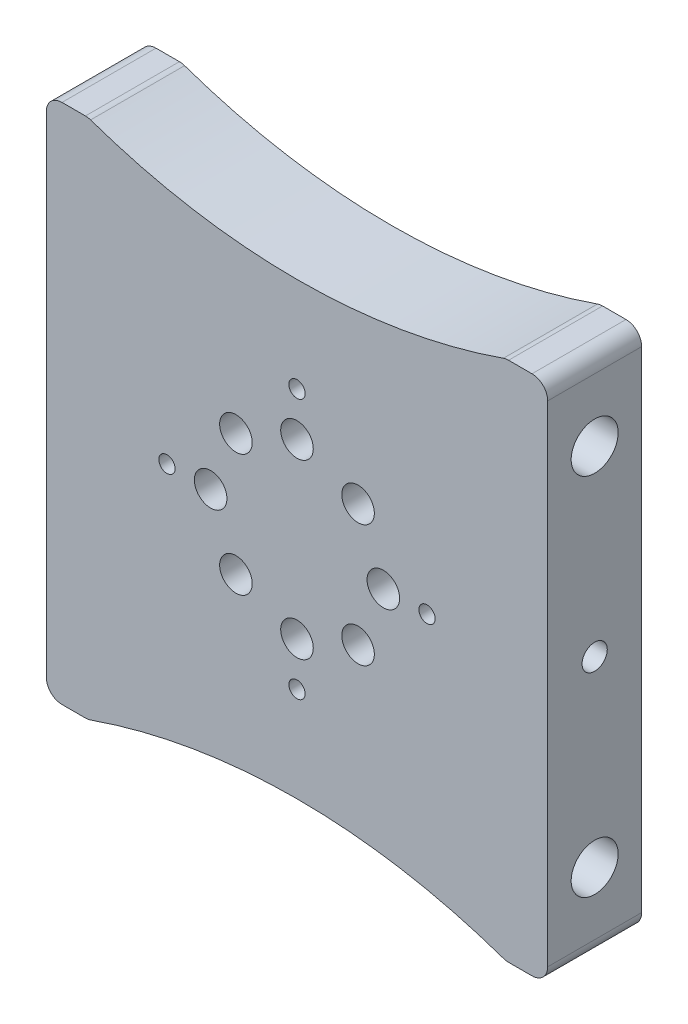
SolidWorks part; units mm, degrees
other "Markup2"
sketch "Sketch39"
material "Onyx"
ref_plane "Front Plane" through (0, 0, 0) normal (0, 0, 1) x (1, 0, 0)
ref_plane "Top Plane" through (0, 0, 0) normal (0, 1, 0) x (1, 0, 0)
ref_plane "Right Plane" through (0, 0, 0) normal (1, 0, 0) x (0, 0, -1)
ref_plane "Plane1" through (0, 0, 0) normal (0, 0, -1) x (-1, 0, 0)
sketch "Sketch1" plane through (0, 0, 0) normal (0, 0, -1) x (-1, 0, 0)
  line L0 (44.45, 0) -> (44.45, 60)
  line L1 (44.45, 60) -> (-44.45, 60)
  line L2 (-44.45, 60) -> (-44.45, 0)
  arc A0 (-44.45, 0) -> (44.45, 0) centre (0, 0) ccw
extrude "Boss-Extrude1" add sketch "Sketch1" against normal blind 19.05
hole_wizard "#4 Clearance Hole1" [suppressed] positions "Sketch3" profile "Sketch2" hole size "#4" standard "ANSI Inch"
sketch "Sketch3" plane through (0, 0, 19.05) normal (0, 0, 1) x (1, 0, 0)
  line L0 (6, 0) -> (6, 26.35) construction
  line L1 (6, 0) -> (32.35, 0) construction
  line L2 (6, 0) -> (6, -26.35) construction
  line L3 (6, 0) -> (-20.35, 0) construction
  circle A0 centre (6, 0) radius 26.35 construction
  point P0 (32.35, 0.009)
  point P1 (6, -26.35)
  point P2 (-20.35, -0.01)
  point P3 (6, 26.35)
  dimension "D1" = 52.7
  dimension "D2" = 6
sketch "Sketch2" plane through (32.35, 0.009, 19.05) normal (1, 0, 0) x (0, -1, 0)
  line L0 (0, 0) -> (0, 19.05)
  line L1 (0, 19.05) -> (1.65, 19.05)
  line L2 (1.65, 19.05) -> (1.65, 0)
  line L5 (1.65, 0) -> (0, 0)
  line L11 (0, -6.35) -> (0, 107.95) construction
  dimension "Thru Hole Dia." = 3.3
  dimension "Thru Hole Depth" = 19.05
hole_wizard "1/4 Clearance Hole1" [suppressed] positions "Sketch5" profile "Sketch4" hole size "1/4" standard "ANSI Inch"
sketch "Sketch5" plane through (0, 0, 0) normal (0, 0, -1) x (-1, 0, 0)
  point P0 (8.85, 30)
  point P1 (23.65, 38)
  point P2 (23.65, 22)
sketch "Sketch4" plane through (-8.85, 30, 0) normal (1, 0, 0) x (0, 1, 0)
  line L0 (0, 0) -> (0, 12.7)
  line L1 (0, 12.7) -> (3.3, 12.7)
  line L2 (3.3, 12.7) -> (3.3, 0)
  line L5 (3.3, 0) -> (0, 0)
  line L11 (0, -6.35) -> (0, 107.95) construction
  dimension "Thru Hole Dia." = 6.6
  dimension "Thru Hole Depth" = 12.7
hole_wizard "1/4 Clearance Hole2" [suppressed] positions "Sketch7" profile "Sketch6" hole size "1/4" standard "ANSI Inch"
sketch "Sketch7" plane through (0, 0, 12.7) normal (0, 0, 1) x (1, 0, 0)
  line L0 (0, 0) -> (0, 60) construction
  line L1 (-44.45, 60) -> (44.45, 60) construction
  point P0 (17.4725, 49.6929)
  dimension "D1" = 17.4725
sketch "Sketch6" plane through (17.4725, 49.6929, 12.7) normal (1, 0, 0) x (0, -1, 0)
  line L0 (0, 0) -> (0, 12.7)
  line L1 (0, 12.7) -> (3.4, 12.7)
  line L2 (3.4, 12.7) -> (3.4, 0)
  line L5 (3.4, 0) -> (0, 0)
  line L11 (0, -6.35) -> (0, 107.95) construction
  dimension "Thru Hole Dia." = 6.8
  dimension "Thru Hole Depth" = 12.7
hole_wizard "CSK for 1/4 Flat Head Machine Screw (100)1" [suppressed] positions "Sketch9" profile "Sketch8" countersink size "1/4" standard "ANSI Inch"
sketch "Sketch9" plane through (0, 0, 0) normal (0, 0, -1) x (-1, 0, 0)
  point P0 (23.65, 54)
  point P1 (38.45, 6)
  point P2 (38.45, 30)
sketch "Sketch8" plane through (-23.65, 54, 0) normal (1, 0, 0) x (0, 1, 0)
  line L0 (0, 0) -> (0, 12.7)
  line L1 (0, 12.7) -> (3.3, 12.7)
  line L2 (3.3, 12.7) -> (3.3, 3)
  line L3 (3.3, 3) -> (6.3, 0)
  line L5 (6.3, 0) -> (0, 0)
  line L6 (-3.3, 3) -> (-6.3, 0) construction
  line L11 (0, -6.35) -> (0, 107.95) construction
  dimension "Thru Hole Dia." = 6.6
  dimension "Thru Hole Depth" = 12.7
  dimension "Near C'Sink Dia." = 12.6
  dimension "Near C'Sink Angle" = 90
hole_wizard "#10 Clearance Hole1" [suppressed] positions "Sketch11" profile "Sketch10" hole size "#10" standard "ANSI Inch"
sketch "Sketch11" plane through (0, 60, 0) normal (0, 1, 0) x (1, 0, 0)
  point P0 (-38.45, -6.35)
  point P1 (-8.85, -6.35)
sketch "Sketch10" plane through (-38.45, 60, 6.35) normal (1, 0, 0) x (0, 0, 1)
  line L0 (0, 0) -> (0, 15)
  line L1 (0, 15) -> (2.5, 15)
  line L2 (2.5, 15) -> (2.5, 0)
  line L5 (2.5, 0) -> (0, 0)
  line L10 (0, 15) -> (-2.5, 15) construction
  line L11 (0, -6.35) -> (0, 107.95) construction
  dimension "Hole Dia." = 5
  dimension "Hole Depth" = 15
  dimension "Drill Angle" = 180
hole_wizard "#10 Clearance Hole2" [suppressed] positions "Sketch13" profile "Sketch12" hole size "#10" standard "ANSI Inch"
sketch "Sketch13" plane through (44.45, 0, 0) normal (1, 0, 0) x (0, 0, -1)
  point P0 (-6.35, 7)
  point P1 (-6.35, 53)
  point P2 (-6.35, 30)
sketch "Sketch12" plane through (44.45, 7, 6.35) normal (0, 1, 0) x (0, 0, -1)
  line L0 (0, 0) -> (0, 10)
  line L1 (0, 10) -> (2.5, 10)
  line L2 (2.5, 10) -> (2.5, 0)
  line L5 (2.5, 0) -> (0, 0)
  line L10 (0, 10) -> (-2.5, 10) construction
  line L11 (0, -6.35) -> (0, 107.95) construction
  dimension "Hole Dia." = 5
  dimension "Hole Depth" = 10
  dimension "Drill Angle" = 180
hole_wizard "1-3/4 Clearance Hole1" positions "Sketch15" profile "Sketch14" hole size "1-3/4" standard "ANSI Inch"
sketch "Sketch15" plane through (0, 0, 0) normal (0, 0, -1) x (-1, 0, 0)
  point P0 (-6, 0)
  dimension "D1" = 6
sketch "Sketch14" plane through (6, 0, 0) normal (1, 0, 0) x (0, 1, 0)
  line L0 (0, 0) -> (0, 5)
  line L1 (0, 5) -> (22.5, 5)
  line L2 (22.5, 5) -> (22.5, 0)
  line L5 (22.5, 0) -> (0, 0)
  line L10 (0, 5) -> (-22.5, 5) construction
  line L11 (0, -6.35) -> (0, 107.95) construction
  dimension "Hole Dia." = 45
  dimension "Hole Depth" = 5
  dimension "Drill Angle" = 180
hole_wizard "1/4 Clearance Hole3" positions "Sketch17" profile "Sketch16" hole size "1/4" standard "ANSI Inch"
sketch "Sketch17" plane through (0, 0, 19.05) normal (0, 0, 1) x (1, 0, 0)
  line L0 (6, 0) -> (6, 17.5) construction
  line L2 (6, 0) -> (-6.3744, 12.3744) construction
  line L4 (6, 0) -> (-11.5, 0) construction
  line L5 (6, 0) -> (-6.3744, -12.3744) construction
  line L6 (6, 0) -> (6, -17.5) construction
  line L7 (6, 0) -> (18.3744, -12.3744) construction
  line L8 (6, 0) -> (23.5, 0) construction
  line L9 (6, 0) -> (18.3744, 12.3744) construction
  circle A0 centre (6, 0) radius 17.5 construction
  point P0 (18.3744, 12.3744)
  point P1 (23.5, -0.0012)
  point P2 (18.3744, -12.3744)
  point P3 (6, -17.5)
  point P4 (-6.3744, -12.3744)
  point P5 (-11.5, 0)
  point P6 (-6.3744, 12.3744)
  point P7 (6, 17.5)
  dimension "D1" = 35
  dimension "D2" = 45
  dimension "D3" = 45
  dimension "D4" = 45
  dimension "D5" = 45
  dimension "D6" = 6
sketch "Sketch16" plane through (18.3744, 12.3744, 19.05) normal (1, 0, 0) x (0, -1, 0)
  line L0 (0, 0) -> (0, 19.05)
  line L1 (0, 19.05) -> (3.3, 19.05)
  line L2 (3.3, 19.05) -> (3.3, 0)
  line L5 (3.3, 0) -> (0, 0)
  line L11 (0, -6.35) -> (0, 107.95) construction
  dimension "Thru Hole Dia." = 6.6
  dimension "Thru Hole Depth" = 19.05
chamfer "Chamfer1" [suppressed] distance 3 angle 45
sketch "Sketch18" plane through (0, 0, 0) normal (0, 0, -1) x (-1, 0, 0)
  line L0 (44.45, 0) -> (-44.45, 0) construction
  line L1 (-44.45, 0) -> (-50.45, 0)
  line L2 (-6, -44.45) -> (0, -44.45)
  arc A0 (-50.45, 0) -> (-6, -44.45) centre (-6, 0) ccw
  arc A1 (-44.45, 0) -> (44.45, 0) centre (0, 0) ccw construction
  arc A2 (-44.45, 0) -> (0, -44.45) centre (0, 0) ccw
  dimension "D1" = 88.9
extrude "Boss-Extrude2" add sketch "Sketch18" against normal up to surface (19.05 mm away) up to face at (21.6744, 12.3744, 19.05)
sketch "Sketch19" plane through (0, 0, 19.05) normal (0, 0, 1) x (1, 0, 0)
  line L0 (50.45, 0) -> (50.45, 60)
  line L1 (-44.45, 60) -> (44.45, 60) construction
  line L2 (50.45, 60) -> (44.45, 60)
  line L3 (44.45, 60) -> (44.45, 0)
  line L4 (44.45, 0) -> (50.45, 0)
sketch "Sketch21" plane through (0, 0, 19.05) normal (0, 0, 1) x (1, 0, 0)
  line L0 (23.5, -0.0012) -> (-11.5, 0) construction
  circle A0 centre (6, -0.0006) radius 30
  arc M14 (-44.45, 0) -> (0, -44.45) centre (0, 0) ccw
  line M15 (0, -44.45) -> (6, -44.45)
  arc M16 (6, -44.45) -> (50.45, 0) centre (6, 0) ccw
  line M17 (50.45, 0) -> (44.45, 0)
  line M18 (44.45, 0) -> (44.45, 60)
  line M19 (44.45, 60) -> (-44.45, 60)
  line M20 (-44.45, 60) -> (-44.45, 0)
extrude "Cut-Extrude1" cut sketch "Sketch21" against normal through all contours A0 M20 M14 M15 M16 M17 M18 M19
sketch "Sketch22" plane through (0, 0, 19.05) normal (0, 0, 1) x (1, 0, 0)
  line L1 (44.1, -30.0006) -> (44.1, 29.9994)
  line L3 (6, 29.9994) -> (6, 42.8553) construction
  line L5 (6, 29.9994) -> (44.1, 29.9994)
  line L6 (6, -30.0006) -> (44.1, -30.0006)
  circle A0 centre (6, -0.0006) radius 30 construction
  arc A1 (6, -30.0006) -> (6, 29.9994) centre (6, -0.0006) ccw
  point P7 (6, 29.9994)
  point P9 (6, -30.0006)
  dimension "D1" = 38.1
extrude "Boss-Extrude5" add sketch "Sketch22" against normal up to surface (19.05 mm away) up to face at (-16.5, 0, 0)
ref_plane "Plane3" through (6, 0, 0) normal (1, 0, 0) x (0, 0, -1)
mirror "Mirror1" about plane through (6, 0, 0) normal (1, 0, 0) of "Boss-Extrude5"
fillet "Fillet1" [suppressed] radius 20
sketch "Sketch25" [suppressed] plane through (44.1, 0, 0) normal (1, 0, 0) x (0, 0, -1)
  point P0 (-12.7, -3.0098)
  point P1 (-12.7, 11.9902)
  point P3 (-12.7, 26.9902)
hole_wizard "Tap Drill for #8-32 Tap1" [suppressed] positions "Sketch26" profile "Sketch27" hole size "#8-32" standard "ANSI Inch"
sketch "Sketch26" [suppressed] plane through (44.1, 0, 0) normal (1, 0, 0) x (0, 0, -1)
  point P0 (-6.35, 14.9994)
  point P3 (-6.35, -0.0006)
  point P6 (-6.35, -15.0006)
sketch "Sketch27" plane through (44.1, 14.9994, 6.35) normal (0, 1, 0) x (0, 0, -1)
  line L0 (0, 0) -> (0, 9)
  line L1 (0, 9) -> (1.7272, 7.9622)
  line L2 (1.7272, 7.9622) -> (1.7272, 0)
  line L5 (1.7272, 0) -> (0, 0)
  line L10 (0, 9) -> (-1.7272, 7.9622) construction
  line L11 (0, -6.35) -> (0, 107.95) construction
  dimension "Hole Dia." = 3.4544
  dimension "Hole Depth" = 9
  dimension "Drill Angle" = 118
mirror "Mirror2" [suppressed] about plane through (6, 0, 0) normal (1, 0, 0)
sketch "Sketch28" plane through (0, 0, 19.05) normal (0, 0, 1) x (1, 0, 0)
  line L0 (38.7989, -30.0006) -> (-26.7989, -30.0006)
  line L1 (-32.1, -30.0006) -> (44.1, -30.0006) construction
  line L2 (44.1, -0.0006) -> (-32.1, -0.0006) construction
  line L4 (38.7989, 29.9994) -> (-26.7989, 29.9994)
  line L5 (44.1, -30.0006) -> (44.1, 29.9994) construction
  line L6 (-32.1, -30.0006) -> (-32.1, 29.9994) construction
  arc A0 (-28.7662, 27.6968) -> (-16.7071, 38.2124) centre (6, 0) ccw construction
  arc A2 (38.7989, -30.0006) -> (-26.7989, -30.0006) centre (6, 0) cw
  arc A3 (38.7989, 29.9994) -> (-26.7989, 29.9994) centre (6, -0.0012) ccw
  line M16 (44.1, 29.9994) -> (-32.1, 29.9994)
  line M18 (-32.1, -30.0006) -> (44.1, -30.0006)
extrude "Boss-Extrude6" add sketch "Sketch28" against normal up to surface (19.05 mm away) contours A3 M16 | A2 M18 up to face at (-16.5, 0, 0)
fillet "Fillet2" radius 13 4 edges at (38.7989, 29.9994, 9.525) (-26.7989, 29.9994, 9.525) (38.7989, -30.0006, 9.525) (-26.7989, -30.0006, 9.525)
sketch "Sketch29" plane through (0, 0, 0) normal (0, 0, 1) x (1, 0, 0)
  line L3 (44.1, 29.9994) -> (56.8, 29.9994)
  line L4 (44.1, 29.9994) -> (44.1, -30.0006)
  line L5 (44.1, -30.0006) -> (56.8, -30.0006)
  line L6 (56.8, 29.9994) -> (56.8, -30.0006)
  line L7 (-32.0979, 29.9994) -> (-44.7979, 29.9994)
  line L8 (-32.0979, 29.9994) -> (-32.0979, -30.0006)
  line L9 (-32.0979, -30.0006) -> (-44.7979, -30.0006)
  line L10 (-44.7979, 29.9994) -> (-44.7979, -30.0006)
  line L13 (-32.1, -30.0006) -> (-32.0979, -30.0006) construction
  dimension "D1" = 12.7
extrude "Boss-Extrude7" add sketch "Sketch29" along normal up to surface (19.05 mm away) up to face at (26.8, -0.0012, 19.05)
sketch "Sketch40" plane through (0, 0, 19.05) normal (0, 0, 1) x (1, 0, 0)
  line L5 (56.8, -30.0006) -> (44.0979, -30.0006)
  line L13 (56.8, -30.0006) -> (56.8, -52.8359)
  line L23 (-44.7979, -30.0006) -> (-32.0979, -30.0006)
  line L24 (-44.7979, -30.0006) -> (-44.7979, -52.8359)
  line L25 (56.8, -52.8359) -> (48.3333, -52.8359)
  line L26 (-36.3312, -52.8359) -> (-44.7979, -52.8359)
  line L27 (56.8, -0.0006) -> (-44.7979, -0.0006) construction
  line L28 (56.8, -30.0006) -> (56.8, 29.9994) construction
  line L29 (-44.7979, -30.0006) -> (-44.7979, 29.9994) construction
  line L30 (-36.3312, 52.8346) -> (-44.7979, 52.8346)
  line L31 (56.8, 52.8346) -> (48.3333, 52.8346)
  line L32 (-44.7979, 29.9994) -> (-44.7979, 52.8346)
  line L33 (-44.7979, 29.9994) -> (-32.0979, 29.9994)
  line L34 (56.8, 29.9994) -> (56.8, 52.8346)
  line L35 (56.8, 29.9994) -> (44.0979, 29.9994)
  arc A12 (48.3333, -52.8359) -> (-36.3312, -52.8359) centre (6.0011, -172.573) ccw
  arc A13 (44.0979, -30.0006) -> (35.477, -33.2703) centre (44.0979, -43.0006) ccw
  arc A14 (-32.0979, -30.0006) -> (-23.477, -33.2703) centre (-32.0979, -43.0006) cw
  arc A15 (-23.477, -33.2703) -> (35.477, -33.2703) centre (6, 0) ccw
  arc A16 (-23.477, 33.269) -> (35.477, 33.269) centre (6, -0.0012) cw
  arc A17 (-32.0979, 29.9994) -> (-23.477, 33.269) centre (-32.0979, 42.9994) ccw
  arc A18 (44.0979, 29.9994) -> (35.477, 33.269) centre (44.0979, 42.9994) cw
  arc A19 (48.3333, 52.8346) -> (-36.3312, 52.8346) centre (6.0011, 172.5717) cw
  dimension "D1" = 8.4667
  dimension "D3" = 127
  dimension "D2" = 8.4667
extrude "Boss-Extrude8" add sketch "Sketch40" against normal up to surface (19.05 mm away) up to face at (6.0004, -0.0006, 0)
fillet "Fillet3" radius 3.175 8 edges at (-44.7979, -52.8359, 9.525) (-36.3312, -52.8359, 9.525) (48.3333, -52.8359, 9.525) (56.8, -52.8359, 9.525) (-44.7979, 52.8346, 9.525) (-36.3312, 52.8346, 9.525) (48.3333, 52.8346, 9.525) (56.8, 52.8346, 9.525)
sketch "Sketch46" plane through (0, 0, 19.05) normal (0, 0, 1) x (1, 0, 0)
  line L0 (56.8, 49.6596) -> (66.325, 49.6596) construction
  line L1 (66.325, 49.6596) -> (66.325, -49.6609) construction
  line L2 (66.325, -49.6609) -> (56.8, -49.6609) construction
  line L3 (56.8, -49.6609) -> (56.8, 49.6596) construction
  line L4 (6.0011, -45.573) -> (6.0011, 45.5717) construction
  arc A0 (47.8289, -52.6587) -> (-35.8268, -52.6587) centre (6.0011, -172.573) ccw construction
  arc A1 (-35.8268, 52.6575) -> (47.8289, 52.6575) centre (6.0011, 172.5717) ccw construction
  dimension "D1" = 9.525
sketch "Sketch47" plane through (56.8, 0, 0) normal (1, 0, 0) x (0, 0, -1)
  line L0 (-9.525, -49.6609) -> (-9.525, 49.6596) construction
  line L1 (-19.05, -49.6609) -> (0, -49.6609) construction
  line L2 (0, 49.6596) -> (-19.05, 49.6596) construction
  point P6 (-9.525, -0.0006)
  point P7 (-9.525, 36.9596)
  point P8 (-9.525, -36.9609)
  dimension "D1" = 12.7
  dimension "D2" = 12.7
hole_wizard "3/8 (0.3750) Dowel Hole1" positions "Sketch48" profile "Sketch49" hole size "3/8" standard "ANSI Inch"
sketch "Sketch48" plane through (56.8, 0, 0) normal (1, 0, 0) x (0, 0, -1)
  point P0 (-9.525, -36.9609)
  point P3 (-9.525, 36.9596)
sketch "Sketch49" plane through (56.8, -36.9609, 9.525) normal (0, 1, 0) x (0, 0, -1)
  line L0 (0, 0) -> (0, 28.2616)
  line L1 (0, 28.2616) -> (4.7625, 25.4)
  line L2 (4.7625, 25.4) -> (4.7625, 0)
  line L5 (4.7625, 0) -> (0, 0)
  line L10 (0, 28.2616) -> (-4.7625, 25.4) construction
  line L11 (0, -6.35) -> (0, 107.95) construction
  dimension "Hole Dia." = 9.525
  dimension "Hole Depth" = 25.4
  dimension "Drill Angle" = 118
mirror "Mirror6" about plane through (6, 0, 0) normal (1, 0, 0) of "3/8 (0.3750) Dowel Hole1"
inserted part "90145A628_18-8 STAINLESS STEEL DOWEL PIN" [suppressed]
move or copy body "Body-Move/Copy2" [suppressed] placed by mates yes
other "Distance2" [suppressed] parameters "D1"=25.4
sketch "Sketch50" plane through (-44.7979, 0, 0) normal (-1, 0, 0) x (0, 0, 1)
  line L0 (9.525, -49.6609) -> (9.525, 49.6596) construction
  line L1 (0, -49.6609) -> (19.05, -49.6609) construction
  line L2 (19.05, 49.6596) -> (0, 49.6596) construction
  point P6 (9.525, -0.0006)
sketch "Sketch51" plane through (0, 0, 0) normal (0, 0, -1) x (-1, 0, 0)
  circle A0 centre (-6, 0) radius 26.35 construction
  point P3 (-6, -26.35)
  point P4 (-32.35, 0)
  point P5 (-6, 26.35)
  point P6 (20.35, 0)
  dimension "D1" = 52.7
hole_wizard "#4 Clearance Hole2" positions "Sketch52" profile "Sketch53" hole size "#4" standard "ANSI Inch" end condition through all
sketch "Sketch52" plane through (0, 0, 0) normal (0, 0, -1) x (-1, 0, 0)
  point P0 (-6, -26.35)
  point P3 (20.35, 0)
  point P6 (-6, 26.35)
  point P9 (-32.35, 0)
sketch "Sketch53" plane through (6, -26.35, 0) normal (1, 0, 0) x (0, 1, 0)
  line L0 (0, 0) -> (0, 19.05)
  line L1 (0, 19.05) -> (1.65, 19.05)
  line L2 (1.65, 19.05) -> (1.65, 0)
  line L5 (1.65, 0) -> (0, 0)
  line L11 (0, -6.35) -> (0, 107.95) construction
  dimension "Thru Hole Dia." = 3.3
  dimension "Thru Hole Depth" = 19.05
sketch "Sketch54" plane through (-44.7979, 0, 0) normal (-1, 0, 0) x (0, 0, 1)
  line L0 (9.525, -49.6609) -> (9.525, 49.6596) construction
  line L1 (0, -49.6609) -> (19.05, -49.6609) construction
  line L2 (19.05, 49.6596) -> (0, 49.6596) construction
  point P6 (9.525, -0.0006)
hole_wizard "Tap Drill for 1/4-20 Tap1" positions "Sketch59" profile "Sketch58" hole size "1/4-20" standard "ANSI Inch"
sketch "Sketch59" plane through (-44.7979, 0, 0) normal (-1, 0, 0) x (0, 0, 1)
  point P0 (9.525, -0.0006)
sketch "Sketch58" plane through (-44.7979, -0.0006, 9.525) normal (0, 1, 0) x (0, 0, 1)
  line L0 (0, 0) -> (0, 14.2338)
  line L1 (0, 14.2338) -> (2.5527, 12.7)
  line L2 (2.5527, 12.7) -> (2.5527, 0)
  line L5 (2.5527, 0) -> (0, 0)
  line L10 (0, 14.2338) -> (-2.5527, 12.7) construction
  line L11 (0, -6.35) -> (0, 107.95) construction
  dimension "Hole Dia." = 5.1054
  dimension "Hole Depth" = 12.7
  dimension "Drill Angle" = 118
sketch "Sketch60" plane through (56.8, 0, 0) normal (1, 0, 0) x (0, 0, -1)
  line L0 (-9.525, -49.6609) -> (-9.525, 49.6596) construction
  line L1 (-19.05, -49.6609) -> (0, -49.6609) construction
  line L2 (0, 49.6596) -> (-19.05, 49.6596) construction
  point P6 (-9.525, -0.0006)
hole_wizard "Tap Drill for 1/4-20 Tap2" positions "Sketch61" profile "Sketch62" hole size "1/4-20" standard "ANSI Inch"
sketch "Sketch61" plane through (56.8, 0, 0) normal (1, 0, 0) x (0, 0, -1)
  point P0 (-9.525, -0.0006)
sketch "Sketch62" plane through (56.8, -0.0006, 9.525) normal (0, 1, 0) x (0, 0, -1)
  line L0 (0, 0) -> (0, 14.2338)
  line L1 (0, 14.2338) -> (2.5527, 12.7)
  line L2 (2.5527, 12.7) -> (2.5527, 0)
  line L5 (2.5527, 0) -> (0, 0)
  line L10 (0, 14.2338) -> (-2.5527, 12.7) construction
  line L11 (0, -6.35) -> (0, 107.95) construction
  dimension "Hole Dia." = 5.1054
  dimension "Hole Depth" = 12.7
  dimension "Drill Angle" = 118
